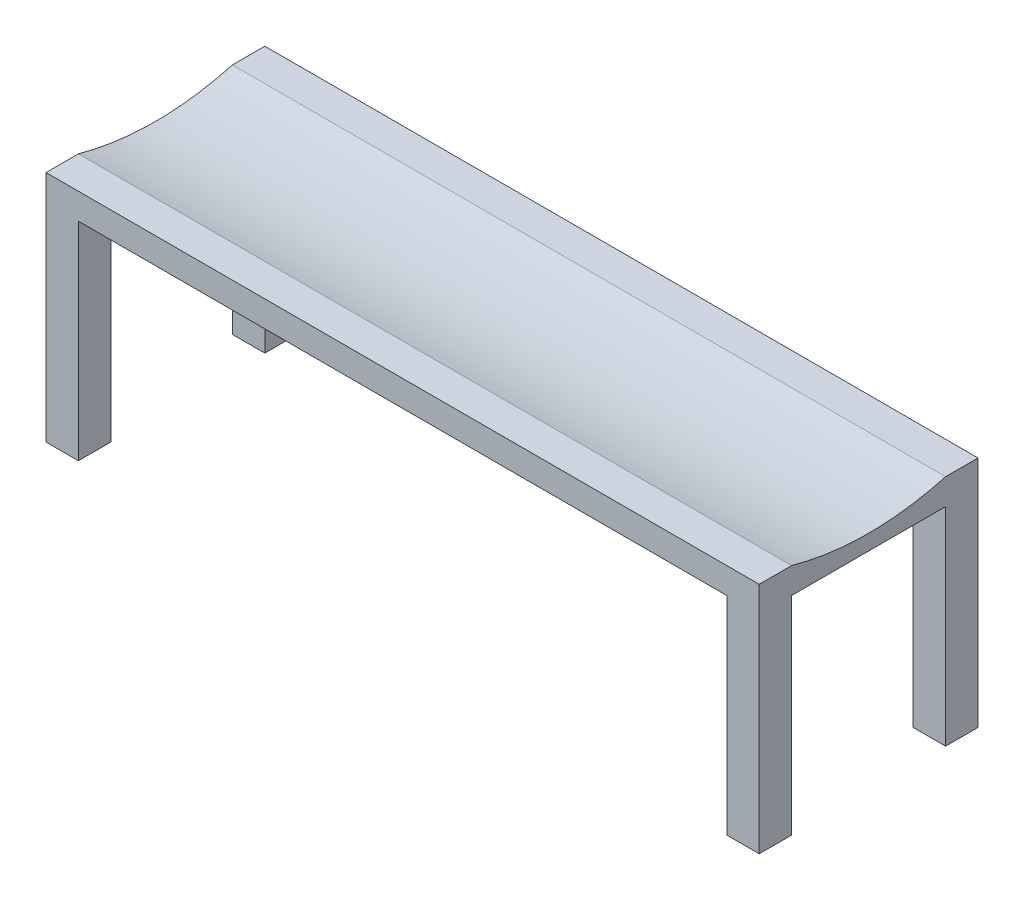
SolidWorks part; units mm, degrees
ref_plane "Front Plane" through (0, 0, 0) normal (0, 0, 1) x (1, 0, 0)
ref_plane "Top Plane" through (0, 0, 0) normal (0, 1, 0) x (1, 0, 0)
ref_plane "Right Plane" through (0, 0, 0) normal (1, 0, 0) x (0, 0, -1)
sketch "Sketch1" plane through (0, 0, 0) normal (0, 1, 0) x (1, 0, 0)
  line L1 (22.688, 6.864) -> (162.388, 6.864)
  line L2 (22.688, 6.864) -> (22.688, 49.7265)
  line L3 (22.688, 49.7265) -> (162.388, 49.7265)
  line L4 (162.388, 6.864) -> (162.388, 49.7265)
extrude "Boss-Extrude1" add sketch "Sketch1" along normal blind 45.72
sketch "Sketch7" plane through (0, 0, 0) normal (0, 1, 0) x (1, 0, 0)
  line L0 (162.388, 13.214) -> (162.388, 43.3765)
  line L1 (22.688, 49.7265) -> (22.688, 6.864) construction
  line L2 (22.688, 43.3765) -> (29.038, 43.3765)
  line L3 (29.038, 43.3765) -> (29.038, 49.7265)
  line L4 (162.388, 49.7265) -> (22.688, 49.7265) construction
  line L5 (162.388, 43.3765) -> (156.038, 43.3765)
  line L6 (162.388, 6.864) -> (162.388, 49.7265) construction
  line L7 (156.038, 43.3765) -> (156.038, 49.7265)
  line L8 (156.038, 49.7265) -> (29.038, 49.7265)
  line L9 (29.038, 6.864) -> (29.038, 13.214)
  line L10 (22.688, 6.864) -> (162.388, 6.864) construction
  line L11 (29.038, 13.214) -> (22.688, 13.214)
  line L12 (29.038, 6.864) -> (156.038, 6.864)
  line L13 (156.038, 6.864) -> (156.038, 13.214)
  line L14 (156.038, 13.214) -> (162.388, 13.214)
  line L15 (162.388, 13.214) -> (162.388, 43.3765)
  line L16 (22.688, 43.3765) -> (22.688, 13.214)
  dimension "D1" = 127
  dimension "D2" = 30.1625
  dimension "D3" = 6.35
extrude "Cut-Extrude2" cut sketch "Sketch7" along normal blind 40.64 contours L2 L16 L11 L9 L12 L13 L14 L0 L5 L7 L8 L3
sketch "Sketch8" plane through (22.688, 0, 0) normal (-1, 0, 0) x (0, 0, 1)
  line L0 (-49.7265, 45.72) -> (-6.864, 45.72) construction
  line L1 (-43.3765, 45.72) -> (-28.2953, 41.581) construction
  line L2 (-28.2953, 41.581) -> (-13.214, 45.72) construction
  spline S0 degree 2 poles (-43.3765, 45.72) (-28.2953, 41.581) (-13.214, 45.72) knots 0 0 0 1 1 1
extrude "Cut-Extrude3" cut sketch "Sketch8" against normal blind 139.7 and the other way through all
